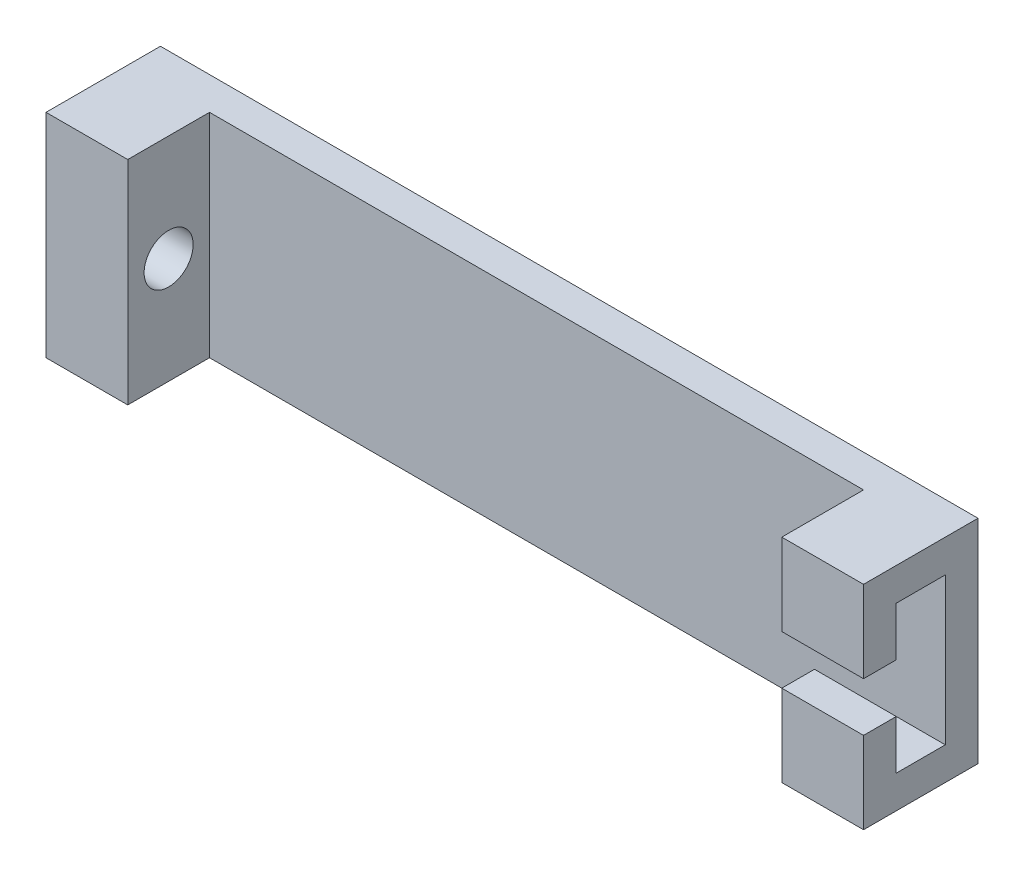
SolidWorks part; units mm, degrees
ref_plane "Front" through (0, 0, 0) normal (0, 0, 1) x (1, 0, 0)
ref_plane "Top" through (0, 0, 0) normal (0, 1, 0) x (1, 0, 0)
ref_plane "Right" through (0, 0, 0) normal (1, 0, 0) x (0, 0, -1)
sketch "Эскиз1" plane through (0, 0, 0) normal (0, 0, 1) x (1, 0, 0)
  line L1 (-25, 6.5) -> (25, 6.5)
  line L2 (-25, 6.5) -> (-25, -6.5)
  line L3 (-25, -6.5) -> (25, -6.5)
  line L4 (25, 6.5) -> (25, -6.5)
  line L5 (-25, 6.5) -> (25, -6.5) construction
  line L6 (-25, -6.5) -> (25, 6.5) construction
  point P0 (0, 0)
  dimension "D1" = 50
  dimension "D2" = 13
extrude "Бобышка-Вытянуть4" add sketch "Эскиз1" along normal blind 2
sketch "Эскиз6" plane through (0, 0, 2) normal (0, 0, 1) x (1, 0, 0)
  line L0 (-25, -6.5) -> (25, -6.5) construction
  line L1 (-25, 6.5) -> (-20, 6.5)
  line L2 (-25, 6.5) -> (-25, -6.5)
  line L3 (-25, -6.5) -> (-20, -6.5)
  line L4 (-20, 6.5) -> (-20, -6.5)
  dimension "D1" = 5
extrude "Бобышка-Вытянуть5" add sketch "Эскиз6" along normal blind 5
sketch "Эскиз7" plane through (-20, 0, 0) normal (1, 0, 0) x (0, 0, -1)
  line L0 (-7, 6.5) -> (-2, 6.5) construction
  line L1 (-7, -6.5) -> (-7, 6.5) construction
  circle A0 centre (-4.5, 0) radius 1.5
  point P4 (0, 0)
  dimension "D3" = 3
  dimension "D1" = 6.5
  dimension "D2" = 2.5
extrude "Вырез-Вытянуть2" cut sketch "Эскиз7" against normal blind 5
sketch "Эскиз8" plane through (0, 0, 2) normal (0, 0, 1) x (1, 0, 0)
  line L0 (-20, -6.5) -> (25, -6.5) construction
  line L1 (25, 6.5) -> (20, 6.5)
  line L2 (25, 6.5) -> (25, -6.5)
  line L3 (25, -6.5) -> (20, -6.5)
  line L4 (20, 6.5) -> (20, -6.5)
  dimension "D1" = 5
extrude "Бобышка-Вытянуть6" add sketch "Эскиз8" along normal blind 5
sketch "Эскиз9" plane through (20, 0, 0) normal (-1, 0, 0) x (0, 0, 1)
  line L0 (2, 6.5) -> (2, -6.5) construction
  line L1 (2, 4.5) -> (5, 4.5)
  line L2 (2, 4.5) -> (2, -4.5)
  line L3 (2, -4.5) -> (5, -4.5)
  line L4 (5, 4.5) -> (5, -4.5)
  line L5 (7, 6.5) -> (2, 6.5) construction
  dimension "D1" = 2
  dimension "D2" = 9
  dimension "D3" = 3
extrude "Вырез-Вытянуть3" cut sketch "Эскиз9" against normal blind 5
sketch "Эскиз10" plane through (20, 0, 0) normal (-1, 0, 0) x (0, 0, 1)
  line L0 (5, -4.5) -> (5, 4.5) construction
  line L1 (5, 1.5) -> (7, 1.5)
  line L2 (5, 1.5) -> (5, -1.5)
  line L3 (5, -1.5) -> (7, -1.5)
  line L4 (7, 1.5) -> (7, -1.5)
  line L5 (7, 6.5) -> (7, -6.5) construction
  line L6 (7, 6.5) -> (2, 6.5) construction
  dimension "D1" = 3
  dimension "D2" = 5
extrude "Вырез-Вытянуть4" cut sketch "Эскиз10" against normal blind 5
